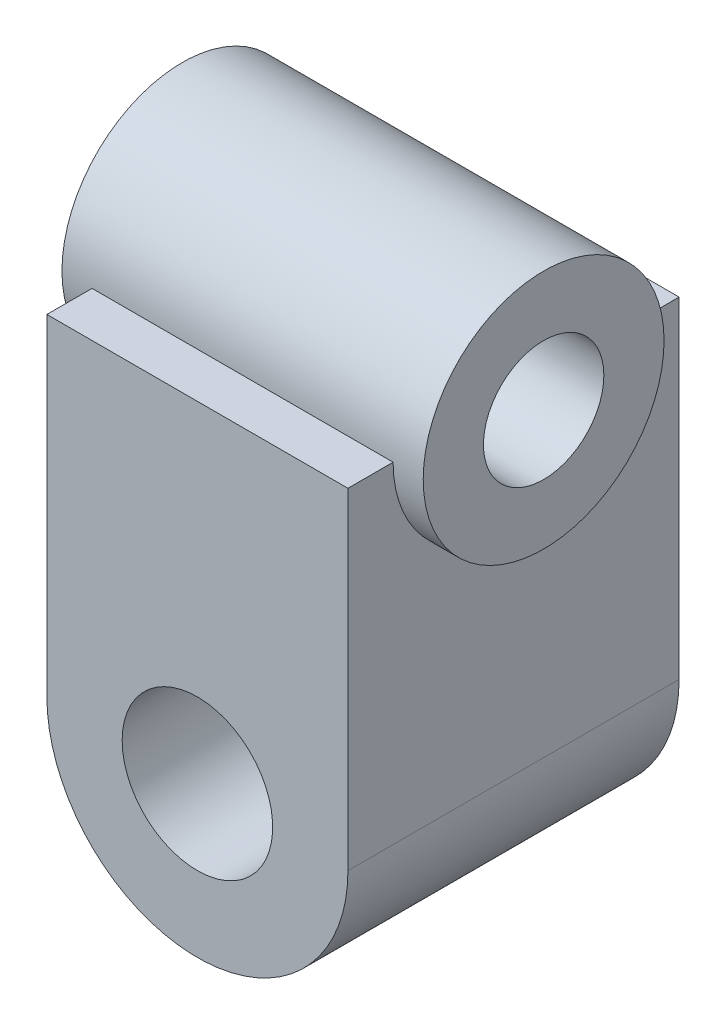
SolidWorks part; units mm, degrees
ref_plane "Front Plane" through (0, 0, 0) normal (0, 0, 1) x (1, 0, 0)
ref_plane "Top Plane" through (0, 0, 0) normal (0, 1, 0) x (1, 0, 0)
ref_plane "Right Plane" through (0, 0, 0) normal (1, 0, 0) x (0, 0, -1)
sketch "Sketch1" plane through (0, 0, 0) normal (0, 0, 1) x (1, 0, 0)
  line L0 (31.75, 0) -> (31.75, 69.85)
  line L1 (-31.75, 0) -> (-31.75, 69.85)
  line L2 (-31.75, 69.85) -> (31.75, 69.85)
  circle A0 centre (0, 0) radius 31.75
  dimension "D1" = 63.5
  dimension "D2" = 69.85
extrude "Boss-Extrude1" add sketch "Sketch1" along normal mid plane 69.85 contours A0 L0 L2 L1 | A0
sketch "Sketch3" plane through (0, 0, 0) normal (1, 0, 0) x (0, 0, -1)
  line L0 (-34.925, 69.85) -> (34.925, 69.85) construction
  circle A0 centre (0, 69.85) radius 25.4
  dimension "D1" = 50.8
extrude "Boss-Extrude2" add sketch "Sketch3" along normal mid plane 76.2
hole_wizard "#97 (1) Diameter Hole1" positions "Sketch4" profile "Sketch5" hole size "#97" standard "ANSI Inch" end condition through all
sketch "Sketch4" plane through (38.1, 0, 0) normal (1, 0, 0) x (0, 0, -1)
  point P0 (0, 69.85)
sketch "Sketch5" plane through (38.1, 69.85, 0) normal (0, 1, 0) x (0, 0, -1)
  line L0 (0, 0) -> (0, 76.2)
  line L1 (0, 76.2) -> (12.7, 76.2)
  line L2 (12.7, 76.2) -> (12.7, 0)
  line L5 (12.7, 0) -> (0, 0)
  line L11 (0, -6.35) -> (0, 107.95) construction
  dimension "Thru Hole Dia." = 25.4
  dimension "Thru Hole Depth" = 76.2
hole_wizard "#97 (1.25) Diameter Hole1" positions "Sketch6" profile "Sketch7" hole size "#97" standard "ANSI Inch" end condition through all
sketch "Sketch6" plane through (0, 0, -34.925) normal (0, 0, -1) x (-1, 0, 0)
  point P0 (0, 0)
sketch "Sketch7" plane through (0, 0, -34.925) normal (1, 0, 0) x (0, 1, 0)
  line L0 (0, 0) -> (0, 69.85)
  line L1 (0, 69.85) -> (15.875, 69.85)
  line L2 (15.875, 69.85) -> (15.875, 0)
  line L5 (15.875, 0) -> (0, 0)
  line L11 (0, -6.35) -> (0, 107.95) construction
  dimension "Thru Hole Dia." = 31.75
  dimension "Thru Hole Depth" = 69.85
